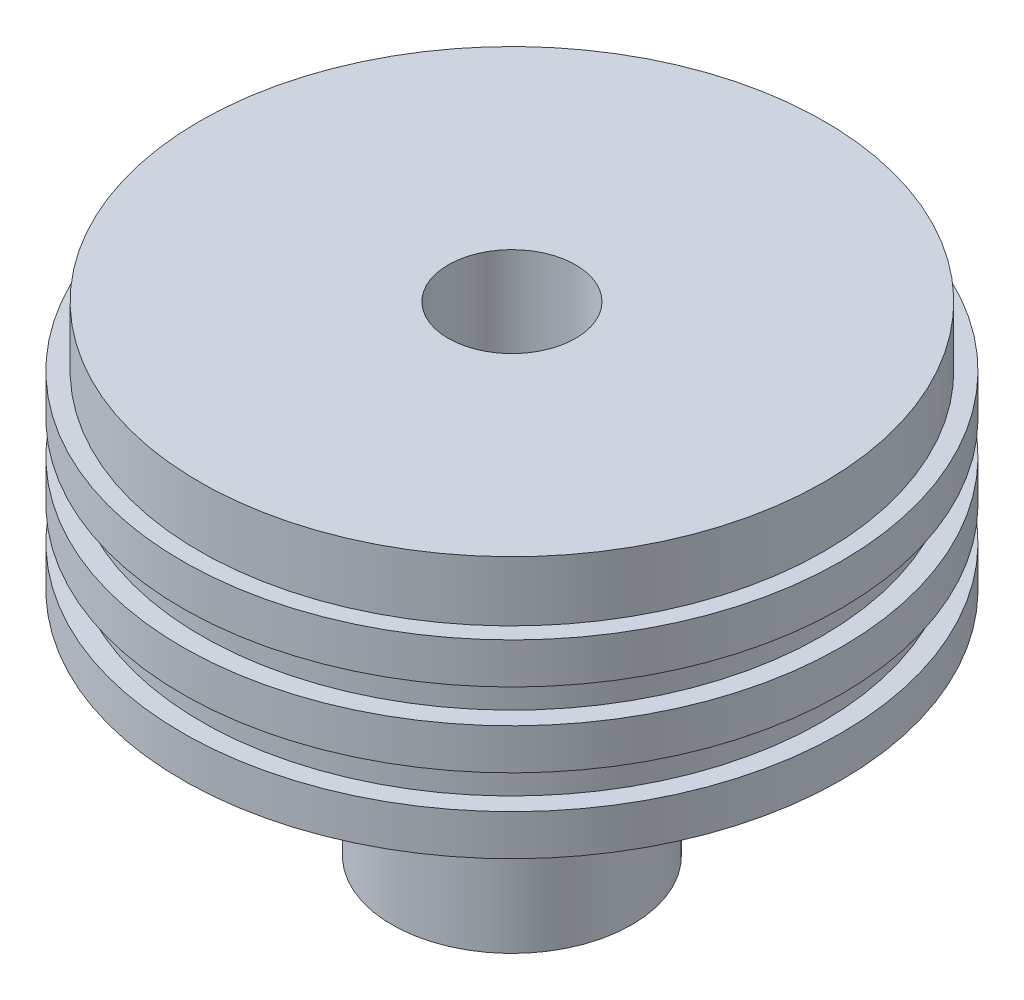
SolidWorks part; units mm, degrees
other "Markup1"
sketch "Sketch11" plane through (34.8996, 26.416, 34.8996) normal (0.3714, 0.4766, 0.7968) x (0.9214, -0.0839, -0.3794)
material "6061-T6 (SS)"
ref_plane "Front Plane" through (0, 0, 0) normal (0, 0, 1) x (1, 0, 0)
ref_plane "Top Plane" through (0, 0, 0) normal (0, 1, 0) x (1, 0, 0)
ref_plane "Right Plane" through (0, 0, 0) normal (1, 0, 0) x (0, 0, -1)
sketch "Sketch8" plane through (0, 0, 0) normal (0, 0, 1) x (1, 0, 0)
  line L0 (0, 0) -> (0, 26.416)
  line L1 (0, 26.416) -> (-33.0835, 26.416)
  line L2 (-33.0835, 26.416) -> (-33.0835, 20.066)
  line L3 (-33.0835, 20.066) -> (-34.8996, 20.066)
  line L4 (-34.8996, 20.066) -> (-34.8996, 15.748)
  line L5 (-34.8996, 15.748) -> (-32.8676, 15.748)
  line L7 (-32.8676, 7.874) -> (-34.8996, 7.874)
  line L8 (-34.8996, 7.874) -> (-34.8996, 12.192)
  line L11 (-32.8676, 4.318) -> (-34.8996, 4.318)
  line L12 (-34.8996, 4.318) -> (-34.8996, 0)
  line L14 (-34.8996, 12.192) -> (-32.8676, 12.192)
  line L15 (-32.8676, 15.748) -> (-32.8676, 12.192)
  line L16 (-32.8676, 7.874) -> (-32.8676, 4.318)
  line L21 (-34.8996, 0) -> (0, 0) construction
  line L22 (0, 0) -> (0, -24.384)
  line L23 (0, -24.384) -> (-12.7, -24.384)
  line L24 (-12.7, -24.384) -> (-12.7, 0)
  line L25 (-12.7, 0) -> (-34.8996, 0)
  dimension "D1" = 6.35
  dimension "D2" = 34.8996
  dimension "D3" = 32.8676
  dimension "D4" = 3.556
  dimension "D5" = 3.556
  dimension "D6" = 4.318
  dimension "D7" = 4.318
  dimension "D8" = 4.318
  dimension "D9" = 33.0835
  dimension "D10" = 12.7
  dimension "D11" = 50.8
revolve "Revolve1" add sketch "Sketch8" angle 360 about L0
hole_wizard "5/8-11 Tapped Hole1" positions "Sketch12" profile "Sketch13" tap size "5/8-11" standard "ANSI Inch" end condition through all
sketch "Sketch12" plane through (0, 26.416, 0) normal (0, 1, 0) x (1, 0, 0)
  point P0 (0, 0)
sketch "Sketch13" plane through (0, 26.416, 0) normal (1, 0, 0) x (0, 0, 1)
  line L0 (0, 0) -> (0, 50.8)
  line L1 (0, 50.8) -> (6.7462, 50.8)
  line L2 (6.7462, 50.8) -> (6.7462, 0)
  line L5 (6.7462, 0) -> (0, 0)
  line L11 (0, -6.35) -> (0, 107.95) construction
  dimension "Thru Tap Drill Dia." = 13.4925
  dimension "Thru Tap Drill Depth" = 50.8
cosmetic thread "Hole Thread1"
